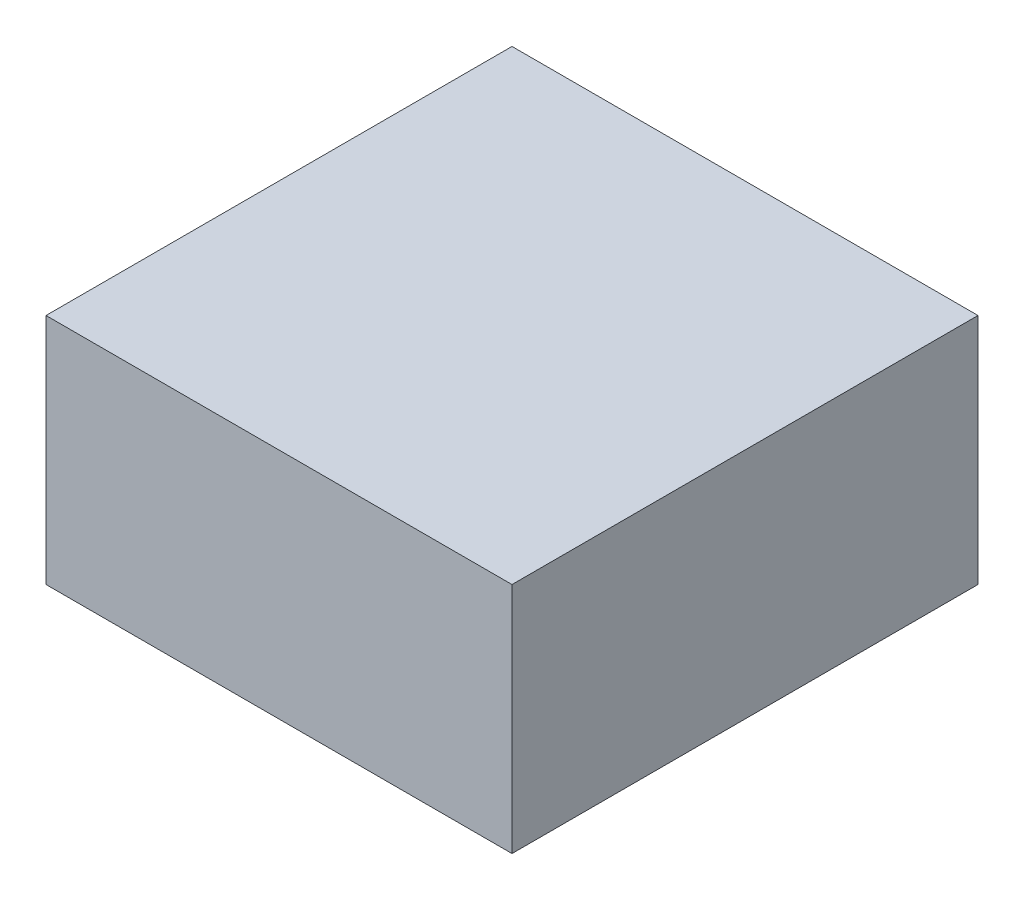
SolidWorks part; units mm, degrees
ref_plane "Front Plane" through (0, 0, 0) normal (0, 0, 1) x (1, 0, 0)
ref_plane "Top Plane" through (0, 0, 0) normal (0, 1, 0) x (1, 0, 0)
ref_plane "Right Plane" through (0, 0, 0) normal (1, 0, 0) x (0, 0, -1)
sketch "Sketch2" plane through (0, 0, 0) normal (0, 1, 0) x (1, 0, 0)
  line L1 (-182.562, 123.2647) -> (71.438, 123.2647)
  line L2 (-182.562, 123.2647) -> (-182.562, -130.7353)
  line L3 (-182.562, -130.7353) -> (71.438, -130.7353)
  line L4 (71.438, 123.2647) -> (71.438, -130.7353)
  dimension "D1" = 254
  dimension "D2" = 254
extrude "Boss-Extrude1" add sketch "Sketch2" along normal blind 127
